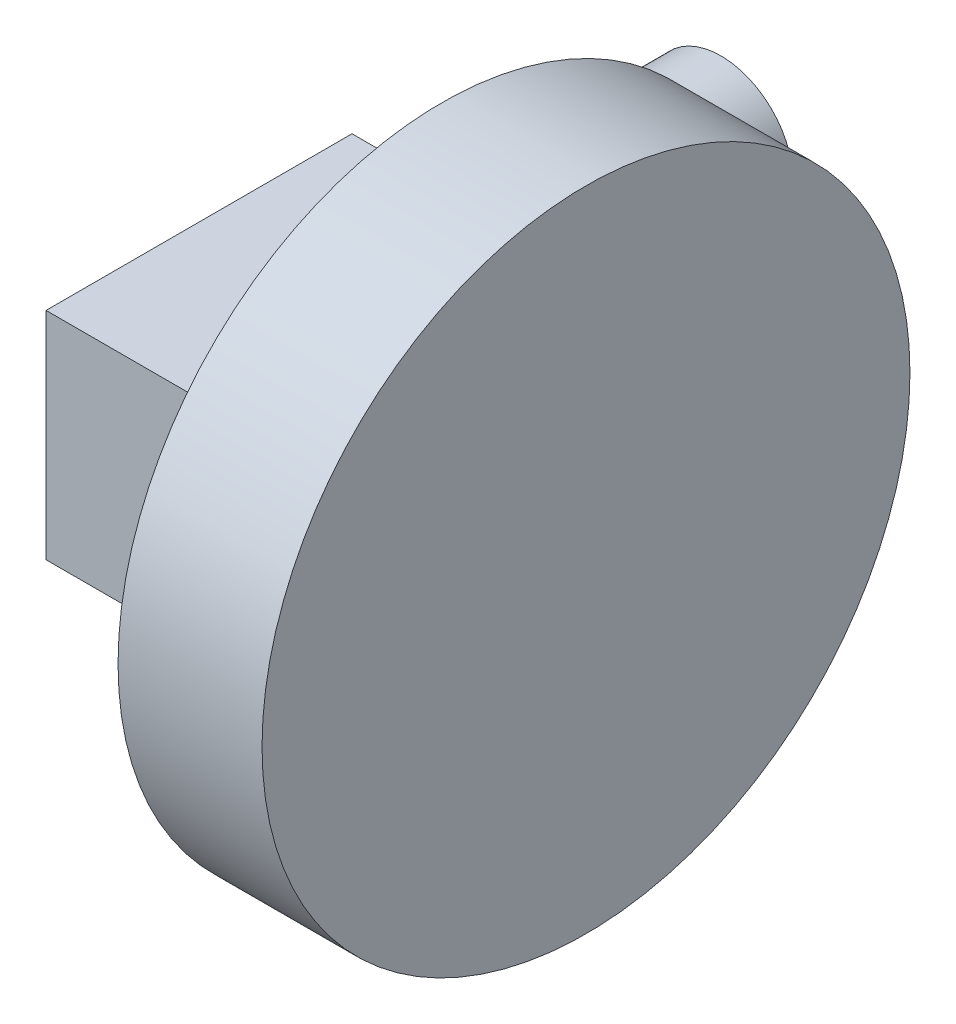
SolidWorks part; units mm, degrees
ref_plane "Front Plane" through (0, 0, 0) normal (0, 0, 1) x (1, 0, 0)
ref_plane "Top Plane" through (0, 0, 0) normal (0, 1, 0) x (1, 0, 0)
ref_plane "Right Plane" through (0, 0, 0) normal (1, 0, 0) x (0, 0, -1)
sketch "Sketch1" plane through (0, 0, 0) normal (1, 0, 0) x (0, 0, -1)
  line L1 (0, 0) -> (170, 0)
  line L2 (0, 0) -> (0, 120)
  line L3 (0, 120) -> (170, 120)
  line L4 (170, 0) -> (170, 120)
  dimension "D1" = 170
  dimension "D2" = 120
extrude "Boss-Extrude1" add sketch "Sketch1" along normal blind 90
sketch "Sketch4" plane through (0, 0, -170) normal (0, 0, -1) x (-1, 0, 0)
  line L0 (-90, 120) -> (0, 0)
  line L1 (0, 0) -> (0, 120)
  line L2 (0, 120) -> (-90, 0)
sketch "Sketch5" plane through (0, 0, -170) normal (0, 0, -1) x (-1, 0, 0)
  line L0 (-90, 120) -> (0, 0) construction
  circle A0 centre (-45, 60) radius 40
  dimension "D1" = 80
extrude "Boss-Extrude3" add sketch "Sketch5" along normal blind 160 contours A0
sketch "Sketch6" plane through (90, 0, 0) normal (1, 0, 0) x (0, 0, -1)
  line L1 (0, 120) -> (80, 120)
  line L2 (0, 120) -> (0, 70)
  line L3 (0, 70) -> (80, 70)
  line L4 (80, 120) -> (80, 70)
  dimension "D1" = 50
  dimension "D2" = 80
sketch "Sketch7" plane through (90, 0, 0) normal (1, 0, 0) x (0, 0, -1)
  circle A0 centre (80, 70) radius 5
  dimension "D1" = 10
extrude "Boss-Extrude4" add sketch "Sketch7" along normal blind 50
sketch "Sketch8" plane through (140, 0, 0) normal (1, 0, 0) x (0, 0, -1)
  circle A0 centre (80, 70) radius 180
  dimension "D1" = 360
extrude "Boss-Extrude5" add sketch "Sketch8" along normal blind 80
